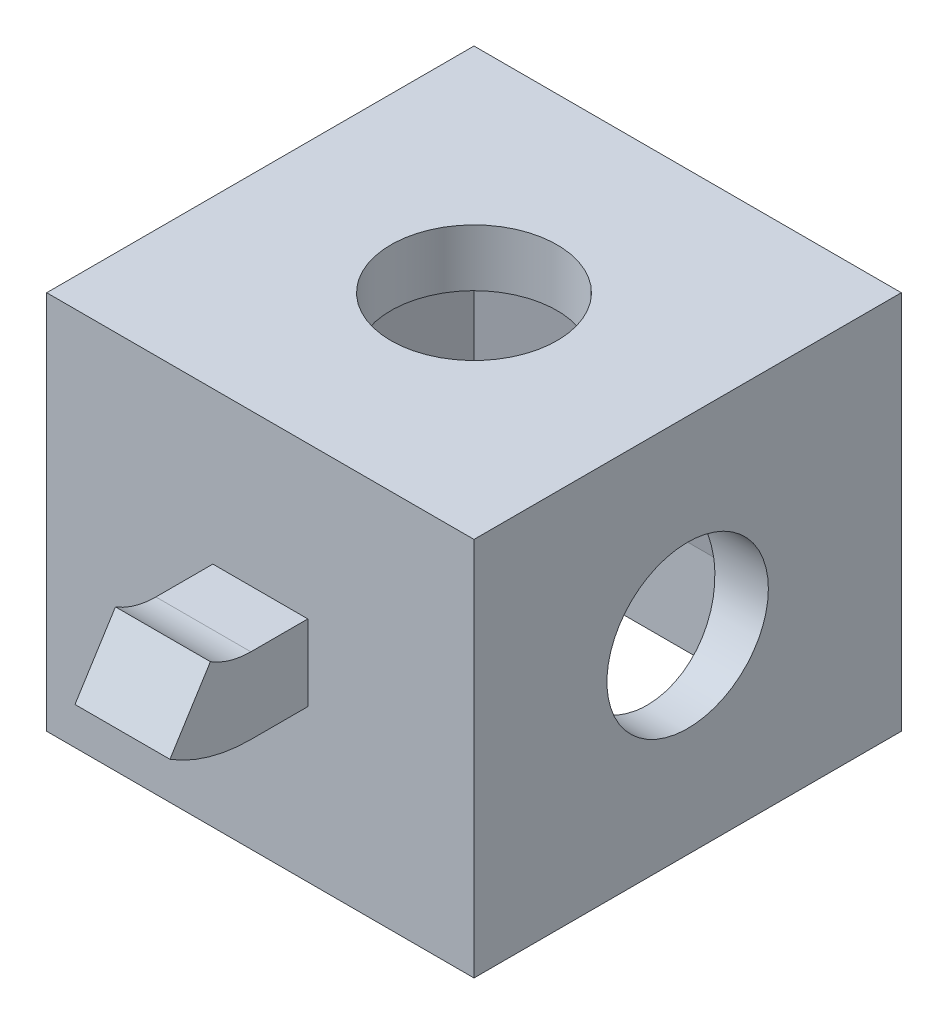
SolidWorks part; units mm, degrees
ref_plane "Front Plane" through (0, 0, 0) normal (0, 0, 1) x (1, 0, 0)
ref_plane "Top Plane" through (0, 0, 0) normal (0, 1, 0) x (1, 0, 0)
ref_plane "Right Plane" through (0, 0, 0) normal (1, 0, 0) x (0, 0, -1)
sketch "Sketch1" plane through (0, 0, 0) normal (0, 1, 0) x (1, 0, 0)
  line L1 (11.25, -11.25) -> (-11.25, -11.25)
  line L2 (11.25, -11.25) -> (11.25, 11.25)
  line L3 (11.25, 11.25) -> (-11.25, 11.25)
  line L4 (-11.25, -11.25) -> (-11.25, 11.25)
  line L5 (11.25, -11.25) -> (-11.25, 11.25) construction
  line L6 (11.25, 11.25) -> (-11.25, -11.25) construction
  point P0 (0, 0)
  dimension "D1" = 22.5
extrude "Boss-Extrude1" add sketch "Sketch1" along normal blind 20
sketch "Sketch2" plane through (0, 20, 0) normal (0, 1, 0) x (1, 0, 0)
  circle A0 centre (0, 0) radius 4.375
  dimension "D1" = 8.75
sketch "Sketch3" plane through (0, 0, 0) normal (0, -1, 0) x (1, 0, 0)
  line L1 (-9.25, -9.25) -> (9.25, -9.25)
  line L2 (-9.25, -9.25) -> (-9.25, 9.25)
  line L3 (-9.25, 9.25) -> (9.25, 9.25)
  line L4 (9.25, -9.25) -> (9.25, 9.25)
  line L5 (-9.25, -9.25) -> (9.25, 9.25) construction
  line L6 (-9.25, 9.25) -> (9.25, -9.25) construction
  point P0 (0, 0)
  dimension "D1" = 18.5
extrude "Cut-Extrude1" cut sketch "Sketch3" against normal blind 12 draft 10 and the other way blind 5 from offset 5 offset against normal yes
extrude "Cut-Extrude2" cut sketch "Sketch2" against normal up to next
sketch "Sketch4" plane through (11.25, 0, 0) normal (1, 0, 0) x (0, 0, -1)
  line L0 (-11.25, 20) -> (11.25, 0) construction
  line L1 (-11.25, 0) -> (11.25, 20) construction
  circle A0 centre (0, 10) radius 4.25
  dimension "D1" = 8.5
extrude "Cut-Extrude3" cut sketch "Sketch4" against normal up to next
sketch "Sketch5" plane through (0, 0, -11.25) normal (0, 0, -1) x (-1, 0, 0)
  line L0 (-11.25, 0) -> (11.25, 20) construction
  line L1 (-11.25, 20) -> (11.25, 0) construction
  line L3 (2.5, 12) -> (-2.5, 12)
  line L4 (2.5, 12) -> (2.5, 8)
  line L5 (2.5, 8) -> (-2.5, 8)
  line L6 (-2.5, 12) -> (-2.5, 8)
  line L7 (2.5, 12) -> (-2.5, 8) construction
  line L8 (2.5, 8) -> (-2.5, 12) construction
  point P8 (0, 10)
  dimension "D1" = 5
  dimension "D2" = 4
sketch "Sketch6" plane through (0, 0, 0) normal (1, 0, 0) x (0, 0, -1)
  line L0 (11.25, 10) -> (14.25, 10)
  arc A0 (14.25, 10) -> (17.4454, 10.9217) centre (14.25, 16) ccw
  dimension "D2" = 6
  dimension "D1" = 3
sweep "Sweep1" add profiles "Sketch5" path "Sketch6"
mirror "Mirror1" about plane through (0, 0, 0) normal (0, 0, 1) of "Sweep1"
